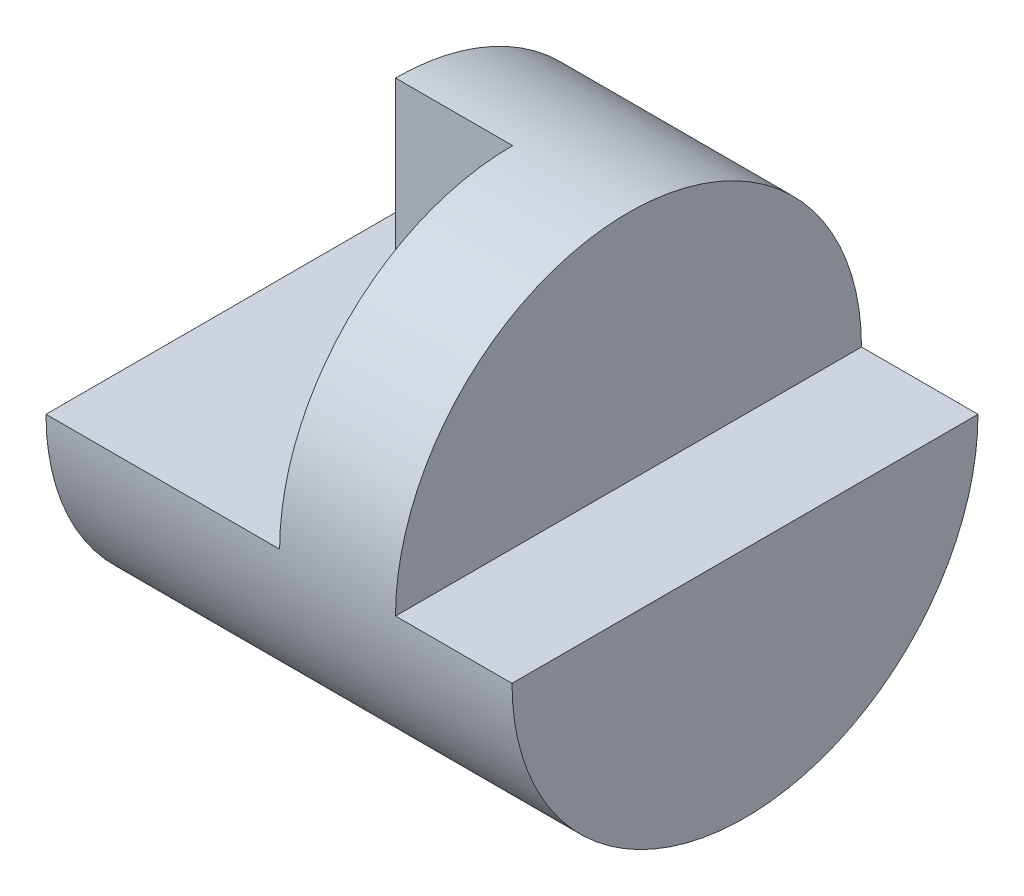
SolidWorks part; units mm, degrees
ref_plane "Front Plane" through (0, 0, 0) normal (0, 0, 1) x (1, 0, 0)
ref_plane "Top Plane" through (0, 0, 0) normal (0, 1, 0) x (1, 0, 0)
ref_plane "Right Plane" through (0, 0, 0) normal (1, 0, 0) x (0, 0, -1)
sketch "Sketch5" plane through (0, 0, 0) normal (0, 0, 1) x (1, 0, 0)
  line L0 (0, 0) -> (4, 0)
  dimension "D1" = 4
revolve "Revolve-Thin2" add sketch "Sketch5" angle 360 about L0 wall 2
sketch "Sketch6" plane through (0, 0, 0) normal (0, 0, 1) x (1, 0, 0)
  line L1 (0, 2) -> (1, 2)
  line L2 (0, 2) -> (0, 0)
  line L3 (0, 0) -> (1, 0)
  line L4 (1, 2) -> (1, 0)
  line L5 (4, 2) -> (3, 2)
  line L6 (4, 2) -> (4, 0)
  line L7 (4, 0) -> (3, 0)
  line L8 (3, 2) -> (3, 0)
  dimension "D1" = 1
  dimension "D2" = 1
  dimension "D3" = 2
  dimension "D4" = 2
extrude "Cut-Extrude5" cut sketch "Sketch6" against normal mid plane 11 contours L5 L8 L7 L6 | L4 L1 L2 L3
sketch "Sketch7" plane through (0, 0, 0) normal (0, 1, 0) x (1, 0, 0)
  line L1 (2.0054, 0) -> (1, 0)
  line L2 (2.0054, 0) -> (2.0054, -2)
  line L3 (2.0054, -2) -> (1, -2)
  line L4 (1, 0) -> (1, -2)
  dimension "D1" = 2
extrude "Cut-Extrude6" cut sketch "Sketch7" along normal blind 3
